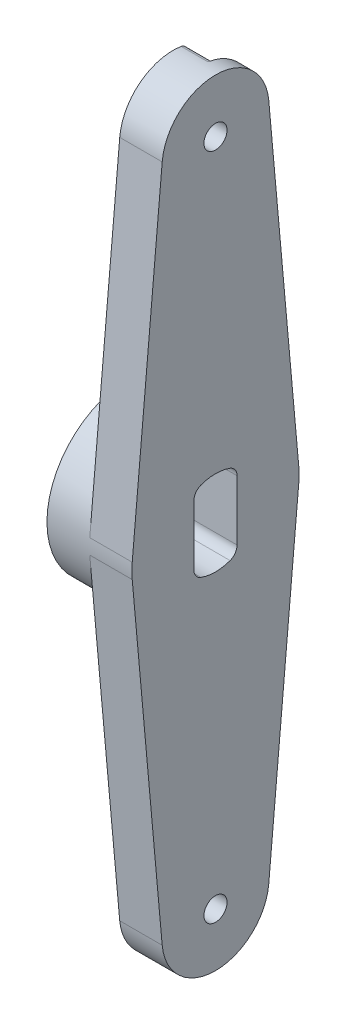
SolidWorks part; units mm, degrees
material "6061-T6 (SS)"
ref_plane "Front Plane" through (0, 0, 0) normal (0, 0, 1) x (1, 0, 0)
ref_plane "Top Plane" through (0, 0, 0) normal (0, 1, 0) x (1, 0, 0)
ref_plane "Right Plane" through (0, 0, 0) normal (1, 0, 0) x (0, 0, -1)
sketch "Sketch1" plane through (0, 0, 0) normal (1, 0, 0) x (0, 0, -1)
  line L0 (0, -50) -> (0, 50) construction
  line L1 (12.4493, 1.125) -> (7.9675, 50.72)
  line L2 (-12.4493, 1.125) -> (-7.9675, 50.72)
  line L3 (0, 0) -> (24.6908, 0) construction
  line L4 (-12.4493, -1.125) -> (-7.9675, -50.72)
  line L5 (12.4493, -1.125) -> (7.9675, -50.72)
  circle A0 centre (0, 0) radius 6.3627
  circle A1 centre (0, 50) radius 5.25
  circle A2 centre (0, 0) radius 12.5
  circle A3 centre (0, 50) radius 3.5
  circle A4 centre (0, 50) radius 8
  circle A5 centre (0, -50) radius 8
  circle A6 centre (0, -50) radius 3.5
  circle A7 centre (0, -50) radius 5.25
  dimension "D1" = 12.7254
  dimension "D2" = 10.5
  dimension "D4" = 25
  dimension "D5" = 7
  dimension "D6" = 16
  dimension "D3" = 50
sketch "Sketch2" plane through (0, 0, 0) normal (1, 0, 0) x (0, 0, -1)
  line L0 (0, 0) -> (28.9178, 0) construction
  line L1 (12.4493, 1.125) -> (7.9675, 50.72) construction
  line L2 (-12.4493, -1.125) -> (-7.9675, -50.72)
  line L3 (12.4493, -1.125) -> (7.9675, -50.72)
  line L5 (-12.4493, 1.125) -> (-7.9675, 50.72) construction
  line L8 (12.4493, 1.125) -> (7.9675, 50.72)
  line L9 (-12.4493, 1.125) -> (-7.9675, 50.72)
  circle A0 centre (0, 0) radius 12.5 construction
  arc A1 (-12.4493, 1.125) -> (-12.4493, -1.125) centre (0, 0) ccw
  arc A2 (12.4493, -1.125) -> (12.4493, 1.125) centre (0, 0) ccw
  circle A3 centre (0, 50) radius 8 construction
  circle A4 centre (0, -50) radius 8 construction
  arc A5 (7.9675, 50.72) -> (-7.9675, 50.72) centre (0, 50) ccw
  arc A6 (-7.9675, -50.72) -> (7.9675, -50.72) centre (0, -50) ccw
extrude "Boss-Extrude1" add sketch "Sketch2" against normal blind 6.35
sketch "Sketch3" plane through (-6.35, 0, 0) normal (-1, 0, 0) x (0, 0, 1)
  line L0 (-4.1186, 56.8584) -> (1.6223, 54.993)
  line L1 (-8.7895, 41.6239) -> (1.6223, 45.007)
  line L2 (-12.4493, 1.125) -> (-7.9675, 50.72) construction
  line L3 (-8.7895, 41.6239) -> (-7.9675, 50.72)
  line L4 (0, 50) -> (-14.0932, 50) construction
  circle A0 centre (0, 50) radius 5.25 construction
  arc A1 (1.6223, 45.007) -> (1.6223, 54.993) centre (0, 50) ccw
  circle A2 centre (0, 50) radius 3.5 construction
  circle A3 centre (0, 50) radius 8 construction
  circle A4 centre (0, 50) radius 3.5
  arc A5 (-4.1186, 56.8584) -> (-7.9675, 50.72) centre (0, 50) ccw
  dimension "D1" = 18
  dimension "D2" = 18
extrude "Cut-Extrude1" cut sketch "Sketch3" against normal blind 4
fillet "Fillet1" radius 1 2 edges at (-4.35, 56.8584, -4.1186) (-4.35, 41.6239, -8.7895)
mirror "Mirror1" about plane through (0, 0, 0) normal (0, 1, 0) of "Cut-Extrude1"
sketch "Sketch4" plane through (-6.35, 0, 0) normal (-1, 0, 0) x (0, 0, 1)
  circle A0 centre (0, 0) radius 12.5 construction
  circle A1 centre (0, 0) radius 12.5
extrude "Boss-Extrude2" add sketch "Sketch4" along normal blind 6.35
sketch "Sketch5" plane through (-12.7, 0, 0) normal (-1, 0, 0) x (0, 0, 1)
  line L0 (-3.2258, 5.4844) -> (-3.2258, -5.4844)
  line L1 (0, -50) -> (0, 50) construction
  line L2 (0, -50) -> (0, 50) construction
  line L3 (3.2258, 5.4844) -> (3.2258, -5.4844)
  circle A0 centre (0, 0) radius 6.3627 construction
  arc A1 (-3.2258, -5.4844) -> (3.2258, -5.4844) centre (0, 0) ccw
  arc A2 (3.2258, 5.4844) -> (-3.2258, 5.4844) centre (0, 0) ccw
  dimension "D1" = 6.4516
extrude "Cut-Extrude2" cut sketch "Sketch5" against normal through all
fillet "Fillet2" radius 1 2 edges at (-4.35, -56.8584, -4.1186) (-4.35, -41.6239, -8.7895)
fillet "Fillet3" radius 1.5875 4 edges at (-6.35, -5.4844, -3.2258) (-6.35, -5.4844, 3.2258) (-6.35, 5.4844, 3.2258) (-6.35, 5.4844, -3.2258)
sketch "Sketch6" plane through (-6.35, 0, 0) normal (-1, 0, 0) x (0, 0, 1)
  circle A0 centre (0, 50) radius 2.54
  circle A1 centre (0, 50) radius 5.5563
  dimension "D1" = 11.1125
  dimension "D2" = 5.08
sketch "Sketch9" plane through (-6.35, 0, 0) normal (-1, 0, 0) x (0, 0, 1)
  circle A1 centre (0, 50) radius 3.5
  circle A2 centre (0, 50) radius 3.5
  dimension "D1" = 0
extrude "Cut-Extrude3" cut sketch "Sketch9" against normal blind 2.2
hole_wizard "#8-32 Tapped Hole1" positions "Sketch8" profile "Sketch7" tap size "#8-32" standard "ANSI Inch"
sketch "Sketch8" plane through (-6.35, 0, 0) normal (-1, 0, 0) x (0, 0, 1)
  point P0 (0, 50)
sketch "Sketch7" plane through (-6.35, 50, 0) normal (0, 1, 0) x (0, 0, 1)
  line L0 (0, 0) -> (0, 13.3278)
  line L1 (0, 13.3278) -> (1.7272, 12.29)
  line L2 (1.7272, 12.29) -> (1.7272, 0)
  line L5 (1.7272, 0) -> (0, 0)
  line L10 (0, 13.3278) -> (-1.7272, 12.29) construction
  line L11 (0, -6.35) -> (0, 107.95) construction
  dimension "Tap Drill Dia." = 3.4544
  dimension "Tap Drill Depth" = 12.29
  dimension "Drill Angle" = 118
cosmetic thread "Hole Thread1" parameters "D1"=6.35, "D2"=4.1656
mirror "Mirror2" about plane through (0, 0, 0) normal (0, 1, 0) of "Cut-Extrude3", "#8-32 Tapped Hole1"
